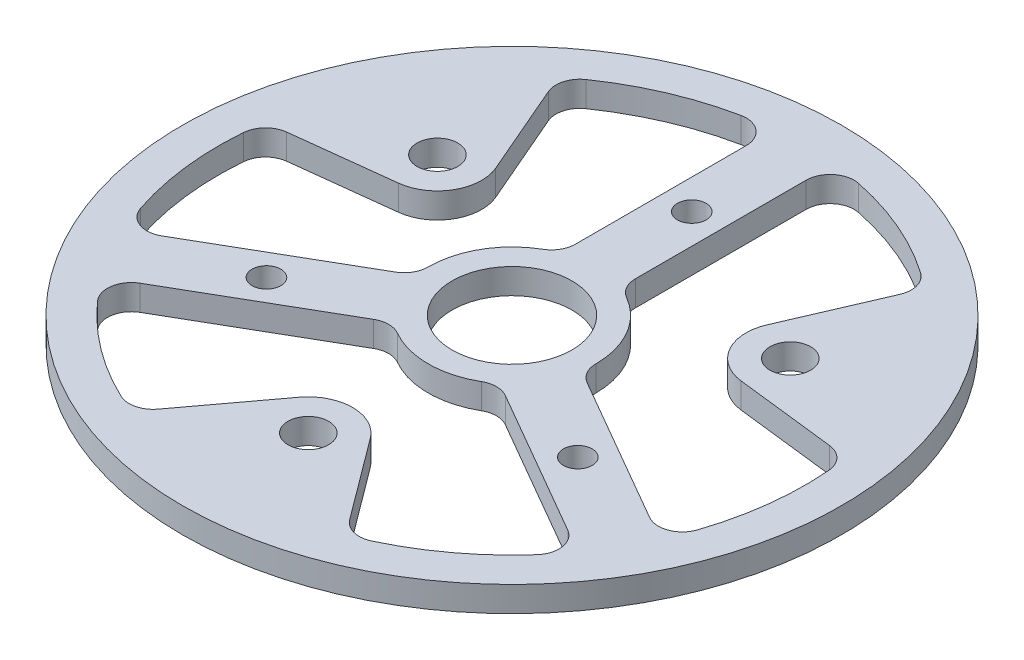
SolidWorks part; units mm, degrees
ref_plane "Alzado" through (0, 0, 0) normal (0, 0, 1) x (1, 0, 0)
ref_plane "Planta" through (0, 0, 0) normal (0, 1, 0) x (1, 0, 0)
ref_plane "Vista lateral" through (0, 0, 0) normal (1, 0, 0) x (0, 0, -1)
sketch "Croquis1" plane through (0, 0, 0) normal (0, 1, 0) x (1, 0, 0)
  circle A0 centre (0, 0) radius 27.5
  dimension "D1" = 55
extrude "Saliente-Extruir1" add sketch "Croquis1" along normal blind 2.11
sketch "Croquis2" plane through (0, 2.11, 0) normal (0, 1, 0) x (1, 0, 0)
  line L0 (0, -27.5) -> (0, 27.5) construction
  line L1 (-27.5, 0) -> (27.5, 0) construction
  line L11 (-2.5, 6.5383) -> (-2.5, 24.3721)
  line L13 (2.5, 6.5383) -> (2.5, 24.3721)
  line L18 (6.9124, -1.1041) -> (22.3569, -10.021)
  line L19 (4.4124, -5.4342) -> (19.8569, -14.3511)
  line L20 (-4.4124, -5.4342) -> (-19.8569, -14.3511)
  line L21 (-6.9124, -1.1041) -> (-22.3569, -10.021)
  line L22 (0, 0) -> (-34.4468, 19.8879) construction
  line L23 (-15.2845, 19.1477) -> (-11.3248, 9.9651)
  line L24 (-24.2246, 3.6629) -> (-14.2924, 4.8251)
  line L25 (24.2246, 3.6629) -> (14.2924, 4.8251)
  line L26 (15.2845, 19.1477) -> (11.3248, 9.9651)
  line L27 (-8.9402, -22.8106) -> (-2.9676, -14.7901)
  line L28 (8.9402, -22.8106) -> (2.9676, -14.7901)
  circle A0 centre (0, 0) radius 27.5 construction
  circle A12 centre (0, 15) radius 1.2
  circle A13 centre (0, 0) radius 15 construction
  circle A14 centre (12.9904, -7.5) radius 1.2
  circle A15 centre (-12.9904, -7.5) radius 1.2
  circle A20 centre (0, 0) radius 5
  arc A21 (-2.5, 24.3721) -> (-15.2845, 19.1477) centre (0, 0) ccw
  circle A22 centre (0, 0) radius 27.5 construction
  arc A23 (-2.5, 6.5383) -> (-6.9124, -1.1041) centre (0, 0) ccw
  arc A24 (6.9124, -1.1041) -> (2.5, 6.5383) centre (0, 0) ccw
  arc A25 (-4.4124, -5.4342) -> (4.4124, -5.4342) centre (0, 0) ccw
  arc A26 (22.3569, -10.021) -> (24.2246, 3.6629) centre (0, 0) ccw
  arc A27 (-19.8569, -14.3511) -> (-8.9402, -22.8106) centre (0, 0) ccw
  circle A28 centre (0, 0) radius 17 construction
  circle A29 centre (-14.7224, 8.5) radius 1.7
  arc A30 (-14.2924, 4.8251) -> (-11.3248, 9.9651) centre (-14.7224, 8.5) ccw
  arc A31 (-24.2246, 3.6629) -> (-22.3569, -10.021) centre (0, 0) ccw
  circle A32 centre (-14.7224, 8.5) radius 3.7 construction
  arc A33 (11.3248, 9.9651) -> (14.2924, 4.8251) centre (14.7224, 8.5) ccw
  circle A34 centre (14.7224, 8.5) radius 1.7
  arc A35 (2.9676, -14.7901) -> (-2.9676, -14.7901) centre (0, -17) ccw
  circle A36 centre (0, -17) radius 1.7
  arc A37 (15.2845, 19.1477) -> (2.5, 24.3721) centre (0, 0) ccw
  arc A38 (8.9402, -22.8106) -> (19.8569, -14.3511) centre (0, 0) ccw
  point P22 (0, 0)
  point P35 (0, 0)
  point P37 (0, 0)
  point P47 (-11.0224, 8.5)
  point P63 (0, 0)
  dimension "D1" = 3
  dimension "D2" = 10
  dimension "D6" = 30
  dimension "D5" = 2.4
  dimension "D4" = 14
  dimension "D10" = 3.4
  dimension "D3" = 5
  dimension "D8" = 3
  dimension "D11" = 60
  dimension "D13" = 10
  dimension "D9" = 2
  dimension "D12" = 2
  dimension "D7" = 3
  dimension "D14" = 3
extrude "Cortar-Extruir1" cut sketch "Croquis2" against normal through all
fillet "Redondeo1" radius 2 18 edges at (-4.4124, 1.055, 5.4342) (4.4124, 1.055, 5.4342) (6.9124, 1.055, 1.1041) (2.5, 1.055, -6.5383) (-6.9124, 1.055, 1.1041) (-2.5, 1.055, -6.5383) (-19.8569, 1.055, 14.3511) (22.3569, 1.055, 10.021) (-2.5, 1.055, -24.3721) (15.2845, 1.055, -19.1477) (24.2246, 1.055, -3.6629) (-15.2845, 1.055, -19.1477) (-24.2246, 1.055, -3.6629) (-22.3569, 1.055, 10.021) (19.8569, 1.055, 14.3511) (-8.9402, 1.055, 22.8106) (8.9402, 1.055, 22.8106) (2.5, 1.055, -24.3721)
